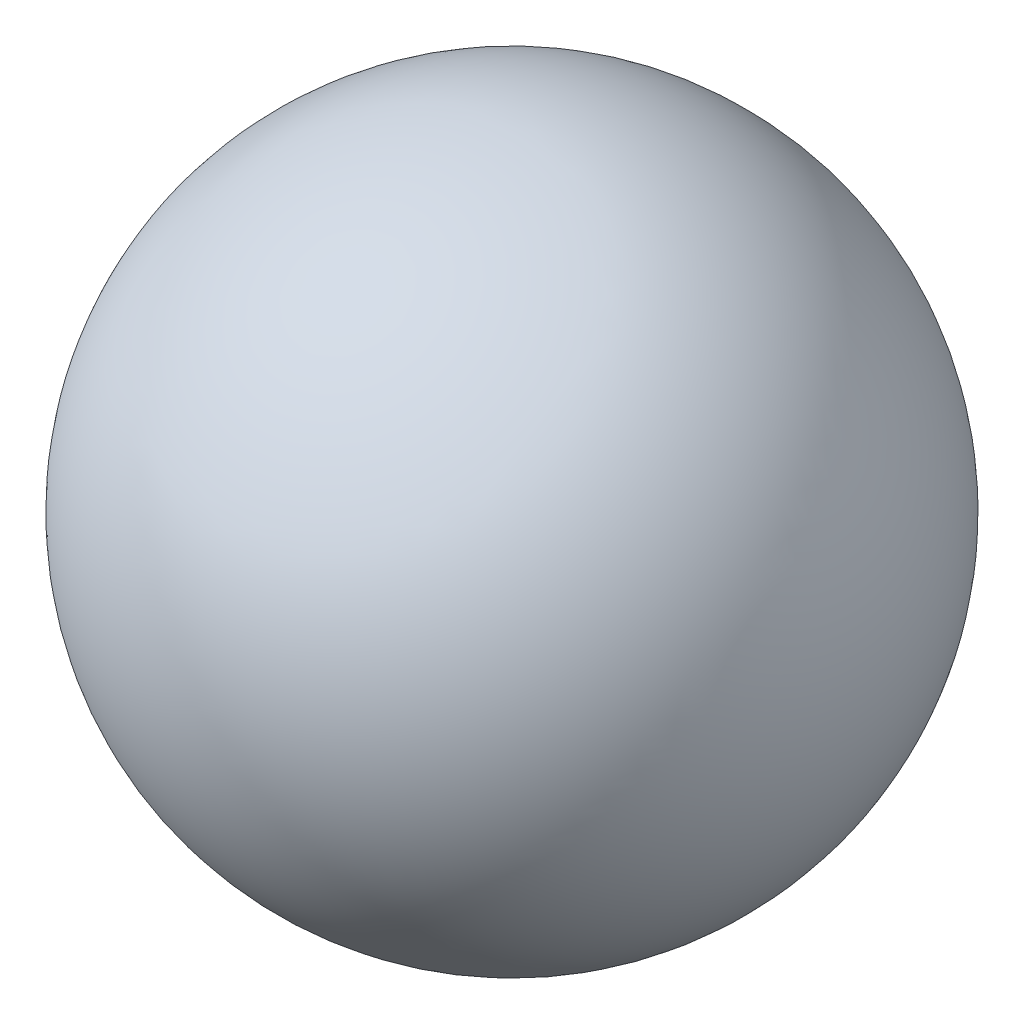
SolidWorks part; units mm, degrees
ref_plane "Front Plane" through (0, 0, 0) normal (0, 0, 1) x (1, 0, 0)
ref_plane "Top Plane" through (0, 0, 0) normal (0, 1, 0) x (1, 0, 0)
ref_plane "Right Plane" through (0, 0, 0) normal (1, 0, 0) x (0, 0, -1)
sketch "Sketch1" plane through (0, 0, 0) normal (0, 0, 1) x (1, 0, 0)
  line L0 (-12.7, 0) -> (12.7, 0)
  arc A0 (12.7, 0) -> (-12.7, 0) centre (0, 0) ccw
  dimension "D1" = 25.4
revolve "Revolve1" add sketch "Sketch1" angle 360 about L0
